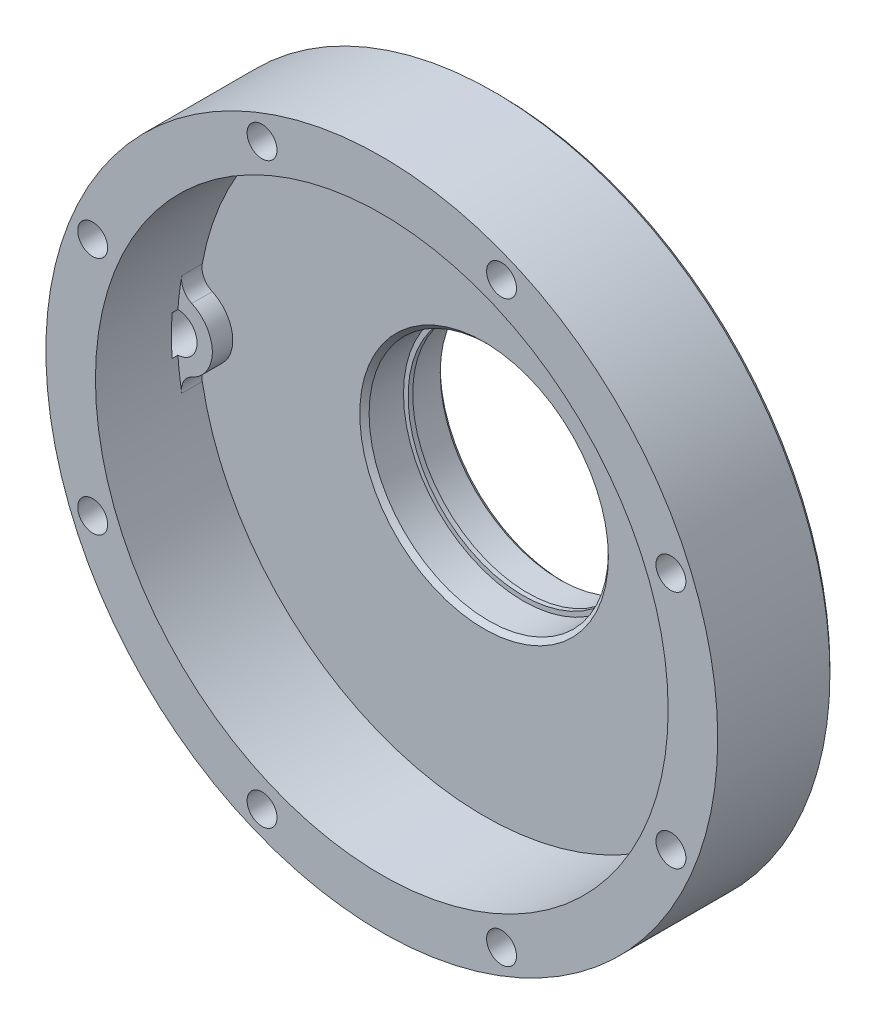
SolidWorks part; units mm, degrees
material "6061-T6 (SS)"
ref_plane "Front Plane" through (0, 0, 0) normal (0, 0, 1) x (1, 0, 0)
ref_plane "Top Plane" through (0, 0, 0) normal (0, 1, 0) x (1, 0, 0)
ref_plane "Right Plane" through (0, 0, 0) normal (1, 0, 0) x (0, 0, -1)
sketch "Motor Plate" plane through (0, 0, 0) normal (0, 0, 1) x (1, 0, 0)
  line L0 (0, 0) -> (0, 60.412) construction
  line L1 (-108.7507, -64.5359) -> (-34.6733, 27.8131)
  line L2 (-119.888, 86.995) -> (118.1354, 86.995) construction
  line L3 (-119.888, 86.995) -> (-119.888, -86.995) construction
  line L4 (-119.888, -86.995) -> (118.1354, -86.995) construction
  line L5 (118.1354, 86.995) -> (118.1354, -86.995) construction
  line L6 (-95.0811, -83.3738) -> (15.6883, -41.5894)
  line L7 (92.7696, -83.9092) -> (-16.1567, -41.4097)
  line L8 (35.159, 27.1965) -> (106.6981, -65.2875)
  line L9 (-119.888, -74.295) -> (118.1354, -74.295) construction
  line L10 (-102.5144, -68.9102) -> (-96.1644, -68.9102) construction
  line L11 (-102.5144, -68.9102) -> (-102.5144, -75.2602)
  line L12 (-102.5144, -75.2602) -> (-96.1644, -75.2602) construction
  line L13 (-96.1644, -68.9102) -> (-96.1644, -75.2602)
  line L14 (-102.5144, -68.9102) -> (-96.1644, -75.2602) construction
  line L15 (-102.5144, -75.2602) -> (-96.1644, -68.9102) construction
  circle A0 centre (0, 0) radius 26 construction
  circle A1 centre (24.7487, 24.7487) radius 3.5
  circle A2 centre (0, 0) radius 35 construction
  circle A3 centre (0, 35) radius 3.5
  circle A4 centre (35, 0) radius 3.5
  circle A5 centre (24.7487, -24.7487) radius 3.5
  circle A6 centre (0, -35) radius 3.5
  circle A7 centre (-24.7487, -24.7487) radius 3.5
  circle A8 centre (-35, 0) radius 3.5
  circle A9 centre (-24.7487, 24.7487) radius 3.5
  circle A10 centre (-99.3394, -72.0852) radius 3.175 construction
  circle A11 centre (97.155, -72.6694) radius 3.175
  circle A12 centre (-119.888, -86.995) radius 12.7 construction
  circle A13 centre (118.1354, -86.995) radius 12.7 construction
  circle A14 centre (-99.3394, -72.0852) radius 12.065
  circle A15 centre (97.155, -72.6694) radius 12.065
  circle A16 centre (0, 0) radius 44.45
  arc A17 (-102.5144, -68.9102) -> (-96.1644, -68.9102) centre (-99.3394, -68.9102) cw
  arc A18 (-102.5144, -75.2602) -> (-96.1644, -75.2602) centre (-99.3394, -75.2602) ccw
  circle A19 centre (-100.4093, -49.0628) radius 3.175
  circle A20 centre (-86.204, -71.12) radius 3.175
  circle A21 centre (0, 0) radius 111.755 construction
  circle A22 centre (-100.4093, -49.0628) radius 6.35
  circle A23 centre (0, 0) radius 103.5 construction
  circle A24 centre (86.204, -71.12) radius 3.175
  circle A25 centre (99.5273, -50.828) radius 3.175
  circle A26 centre (99.5273, -50.828) radius 6.35
  point P23 (0, 0)
  dimension "D1" = 52
  dimension "D2" = 70
  dimension "D3" = 7
  dimension "D9" = 6.35
  dimension "D10" = 25.4
  dimension "D15" = 24.13
  dimension "D16" = 88.9
  dimension "D18" = 3.175
  dimension "D19" = 3.175
  dimension "D20" = 207
  dimension "D22" = 6.35
  dimension "D5" = 238.0234
  dimension "D6" = 173.99
  dimension "D7" = 119.888
  dimension "D8" = 86.995
  dimension "D11" = 14.9098
  dimension "D12" = 20.5486
  dimension "D13" = 20.9804
  dimension "D14" = 14.3256
  dimension "D17" = 6.35
  dimension "D21" = 8.255
  dimension "D4" = 8
sketch "Planetary Plate" plane through (0, 0, 0) normal (0, 0, 1) x (1, 0, 0)
  line L0 (0, 0) -> (0, 82.7651) construction
  line L1 (0, 0) -> (35.7297, 86.2592) construction
  line L2 (-119.888, -74.295) -> (118.1354, -74.295) construction
  line L3 (-119.888, 86.995) -> (-119.888, -86.995) construction
  line L4 (118.1354, 86.995) -> (118.1354, -86.995) construction
  line L5 (-107.188, -86.995) -> (-107.188, 86.995) construction
  line L6 (-119.888, -86.995) -> (118.1354, -86.995) construction
  line L7 (-119.888, 86.995) -> (118.1354, 86.995) construction
  line L8 (105.4354, -86.995) -> (105.4354, 86.995) construction
  line L9 (-67.1006, -19.0261) -> (-107.188, -43.5314) construction
  line L10 (67.4069, -19.2229) -> (105.4354, -44.8551) construction
  line L11 (-107.188, -43.5314) -> (-107.188, -74.295) construction
  line L12 (-107.188, -74.295) -> (-107.188, -86.995) construction
  line L13 (105.4354, -74.295) -> (105.4354, -44.8551) construction
  line L14 (-107.188, -86.995) -> (105.4354, -86.995) construction
  line L15 (105.4354, -86.995) -> (105.4354, -74.295)
  circle A0 centre (0, 0) radius 68 construction
  circle A1 centre (26.0225, 62.8238) radius 3.25
  circle A2 centre (62.8238, 26.0225) radius 3.25
  circle A3 centre (62.8238, -26.0225) radius 3.25
  circle A4 centre (26.0225, -62.8238) radius 3.25
  circle A5 centre (-26.0225, -62.8238) radius 3.25
  circle A6 centre (-62.8238, -26.0225) radius 3.25
  circle A7 centre (-62.8238, 26.0225) radius 3.25
  circle A8 centre (-26.0225, 62.8238) radius 3.25
  circle A9 centre (0, 0) radius 76.2 construction
  circle A10 centre (0, 0) radius 59.8 construction
  circle A11 centre (-119.888, -86.995) radius 12.7 construction
  circle A12 centre (118.1354, -86.995) radius 12.7 construction
  circle A13 centre (-100.4093, -49.0628) radius 3.175
  circle A14 centre (-86.204, -71.12) radius 3.175 construction
  circle A15 centre (99.5273, -50.828) radius 3.175
  circle A16 centre (86.204, -71.12) radius 3.175 construction
  circle A17 centre (-62.8238, -26.0225) radius 8.2 construction
  circle A18 centre (62.8238, -26.0225) radius 8.2 construction
  circle A19 centre (-100.4093, -49.0628) radius 8.255 construction
  circle A20 centre (99.5273, -50.828) radius 8.255 construction
  arc A21 (-67.1006, -19.0261) -> (-55.248, -22.8845) centre (-62.8238, -26.0225) cw construction
  arc A22 (-55.248, -22.8845) -> (55.2943, -22.7725) centre (0, 0) ccw construction
  arc A23 (55.2943, -22.7725) -> (67.4069, -19.2229) centre (62.7734, -25.8527) cw construction
  point P24 (0, 0)
  dimension "D1" = 136
  dimension "D3" = 6.5
  dimension "D5" = 152.4
  dimension "D6" = 6.35
  dimension "D2" = 22.5
  dimension "D7" = 5.08
  dimension "D4" = 8
sketch "Sketch2" plane through (0, 0, 0) normal (1, 0, 0) x (0, 0, -1)
  line L0 (-6.1075, 73) -> (18.2765, 73)
  line L1 (24.605, 20) -> (24.605, -20) construction
  line L2 (24.605, 26) -> (17.1335, 26)
  line L3 (24.605, 26) -> (24.605, 25)
  line L4 (24.605, 25) -> (25.605, 25)
  line L5 (25.605, 25) -> (25.605, 26)
  line L6 (25.605, 26) -> (32.589, 26)
  line L7 (33.605, 27.016) -> (33.605, 31.334)
  line L8 (32.589, 32.35) -> (22.4675, 32.35)
  line L9 (16.1175, 27.016) -> (16.1175, 62.23)
  line L10 (16.1175, 62.23) -> (-6.1075, 62.23)
  line L11 (0, 0) -> (74.9774, 0) construction
  line L12 (17.1335, 26) -> (16.1175, 27.016)
  line L13 (-6.1075, 62.23) -> (-6.1075, 73)
  line L14 (19.2925, 35.525) -> (19.2925, 71.984)
  line L16 (32.589, 26) -> (33.605, 27.016)
  line L17 (33.605, 31.334) -> (32.589, 32.35)
  line L19 (16.1175, 62.23) -> (11.6725, 62.23)
  line L20 (16.1175, 62.23) -> (16.1175, 54.61)
  line L21 (16.1175, 54.61) -> (11.6725, 54.61)
  line L22 (11.6725, 62.23) -> (11.6725, 54.61)
  line L24 (19.2925, 71.984) -> (18.2765, 73)
  arc A0 (19.2925, 35.525) -> (22.4675, 32.35) centre (22.4675, 35.525) ccw
  point P6 (16.1175, 26)
  point P9 (19.2925, 73)
  point P18 (33.605, 26)
  point P21 (33.605, 32.35)
  point P27 (11.6725, 54.61)
  dimension "D8" = 1
  dimension "D9" = 8
  dimension "D11" = 7.62
  dimension "D12" = 7.62
  dimension "D10" = 3.175
  dimension "D1" = 26
  dimension "D2" = 1
  dimension "D3" = 73
  dimension "D4" = 62.23
  dimension "D5" = 3.175
  dimension "D6" = 22.225
  dimension "D7" = 6.35
revolve "Revolve1" add sketch "Sketch2" angle 360 about L11
extrude "Cut-Extrude2" cut sketch "Planetary Plate" against normal through all both and the other way through all contours A6 | A5 | A4 | A7 | A8 | A1 | A2 | A3
sketch "Sketch3" plane through (0, 0, -19.2925) normal (0, 0, -1) x (-1, 0, 0)
  circle A0 centre (0, 62.23) radius 4.3053
  circle A1 centre (62.23, 0) radius 4.3053
  circle A3 centre (0, 0) radius 62.23 construction
  dimension "D1" = 8.6106
extrude "Cut-Extrude3" cut sketch "Sketch3" against normal blind 8.89
sketch "Sketch5" plane through (0, 0, -11.6725) normal (0, 0, 1) x (1, 0, 0)
  arc A0 (-11.0777, 61.2361) -> (-61.2361, 11.0777) centre (0, 0) ccw
  arc A1 (-59.068, -6.933) -> (-59.068, 6.933) centre (-62.23, 0) ccw
  arc A2 (-4.3027, 62.0811) -> (4.3027, 62.0811) centre (0, 62.23) ccw construction
  circle A3 centre (0, 0) radius 54.61
  arc A4 (-6.933, 59.068) -> (6.933, 59.068) centre (0, 62.23) ccw
  arc A5 (-61.2361, -11.0777) -> (11.0777, 61.2361) centre (0, 0) ccw
  arc A6 (-61.2361, 11.0777) -> (-59.068, 6.933) centre (-57.4869, 10.3994) ccw
  arc A7 (-59.068, -6.933) -> (-61.2361, -11.0777) centre (-57.4869, -10.3994) ccw
  arc A8 (11.0777, 61.2361) -> (6.933, 59.068) centre (10.3994, 57.4869) ccw
  arc A9 (-11.0777, 61.2361) -> (-6.933, 59.068) centre (-10.3994, 57.4869) cw
  circle A10 centre (0, 0) radius 54.61 construction
  arc A11 (-62.0811, -4.3027) -> (-62.0811, 4.3027) centre (-62.23, 0) ccw construction
  arc A12 (-62.0811, -4.3027) -> (-62.0811, 4.3027) centre (-62.23, 0) ccw
  arc A13 (-4.3027, 62.0811) -> (4.3027, 62.0811) centre (0, 62.23) ccw
  point P14 (-61.7635, -7.6057)
  dimension "D1" = 3.81
extrude "Cut-Extrude4" cut sketch "Sketch5" against normal up to surface (4.445 mm away)
